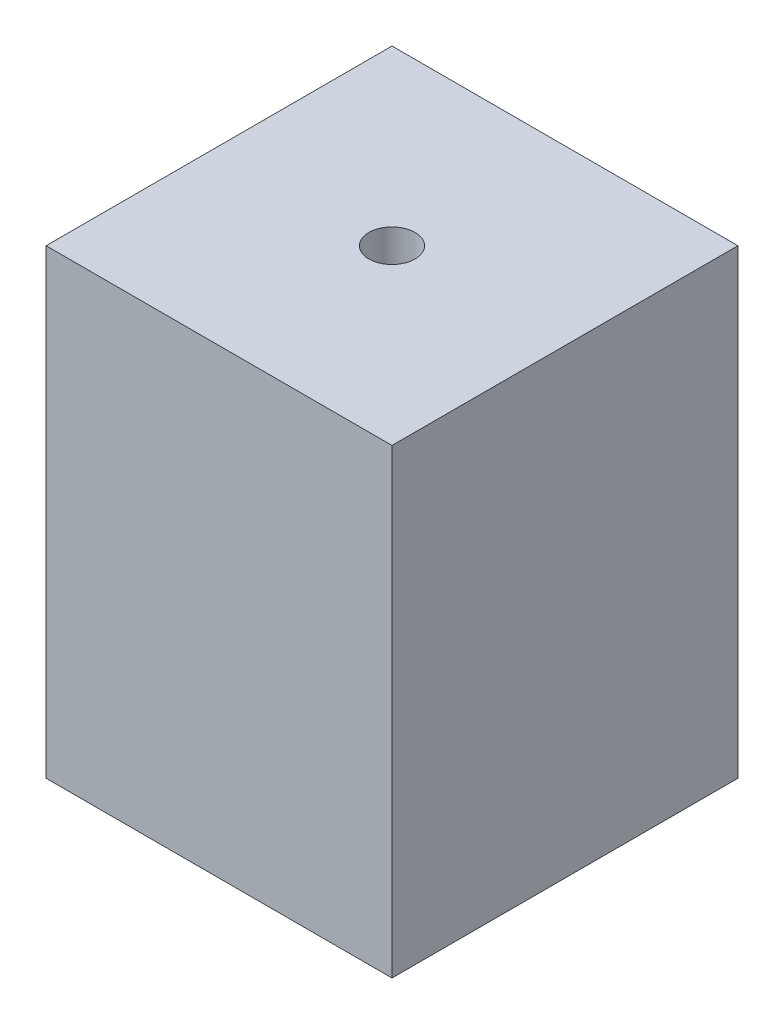
SolidWorks part; units mm, degrees
ref_plane "Front Plane" through (0, 0, 0) normal (0, 0, 1) x (1, 0, 0)
ref_plane "Top Plane" through (0, 0, 0) normal (0, 1, 0) x (1, 0, 0)
ref_plane "Right Plane" through (0, 0, 0) normal (1, 0, 0) x (0, 0, -1)
sketch "Sketch1" plane through (0, 0, 0) normal (0, 1, 0) x (1, 0, 0)
  line L0 (19.05, 38.1) -> (19.05, 0) construction
  line L1 (0, 0) -> (38.1, 0)
  line L2 (0, 0) -> (0, 38.1)
  line L3 (0, 38.1) -> (38.1, 38.1)
  line L4 (38.1, 0) -> (38.1, 38.1)
  line L5 (0, 19.05) -> (38.1, 19.05) construction
  dimension "D1" = 38.1
  dimension "D2" = 38.1
extrude "Boss-Extrude1" add sketch "Sketch1" along normal blind 50.8
sketch "Sketch2" plane through (0, 50.8, 0) normal (0, 1, 0) x (1, 0, 0)
  line L0 (19.05, 0) -> (19.05, 38.1) construction
  line L1 (0, 0) -> (38.1, 0) construction
  line L2 (38.1, 38.1) -> (0, 38.1) construction
  line L3 (0, 19.05) -> (38.1, 19.05) construction
  line L4 (0, 38.1) -> (0, 0) construction
  line L5 (38.1, 0) -> (38.1, 38.1) construction
  circle A0 centre (19.05, 19.05) radius 2.54
  dimension "D1" = 5.08
extrude "Cut-Extrude1" cut sketch "Sketch2" against normal blind 6.35 contours A0
